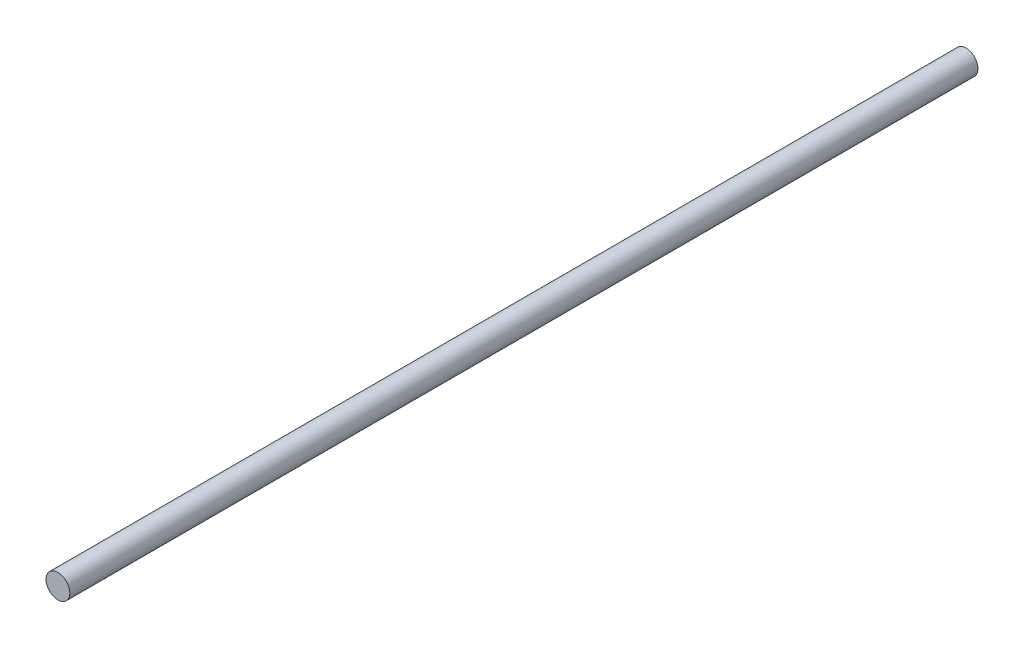
SolidWorks part; units mm, degrees
ref_plane "Front Plane" through (0, 0, 0) normal (0, 0, 1) x (1, 0, 0)
ref_plane "Top Plane" through (0, 0, 0) normal (0, 1, 0) x (1, 0, 0)
ref_plane "Right Plane" through (0, 0, 0) normal (1, 0, 0) x (0, 0, -1)
sketch "Sketch1" plane through (0, 0, 0) normal (0, 0, 1) x (1, 0, 0)
  line L1 (-0.625, 0) -> (0.625, 0) construction
  dimension "OD" = 1.25
sketch "Sketch2" plane through (0, 0, 0) normal (1, 0, 0) x (0, 0, -1)
  line L0 (23.8125, 0) -> (-23.8125, 0)
  point P4 (0, 0)
  dimension "Length" = 47.625
sketch "Sketch3" plane through (0, 0, 0) normal (0, 0, 1) x (1, 0, 0)
  circle A0 centre (0, 0) radius 0.625
extrude "Boss-Extrude1" add sketch "Sketch3" along normal up to vertex (23.8125 mm away) and the other way up to vertex (23.8125 mm away) up to point (0, 0, 23.8125) other way up to point (0, 0, -23.8125)
